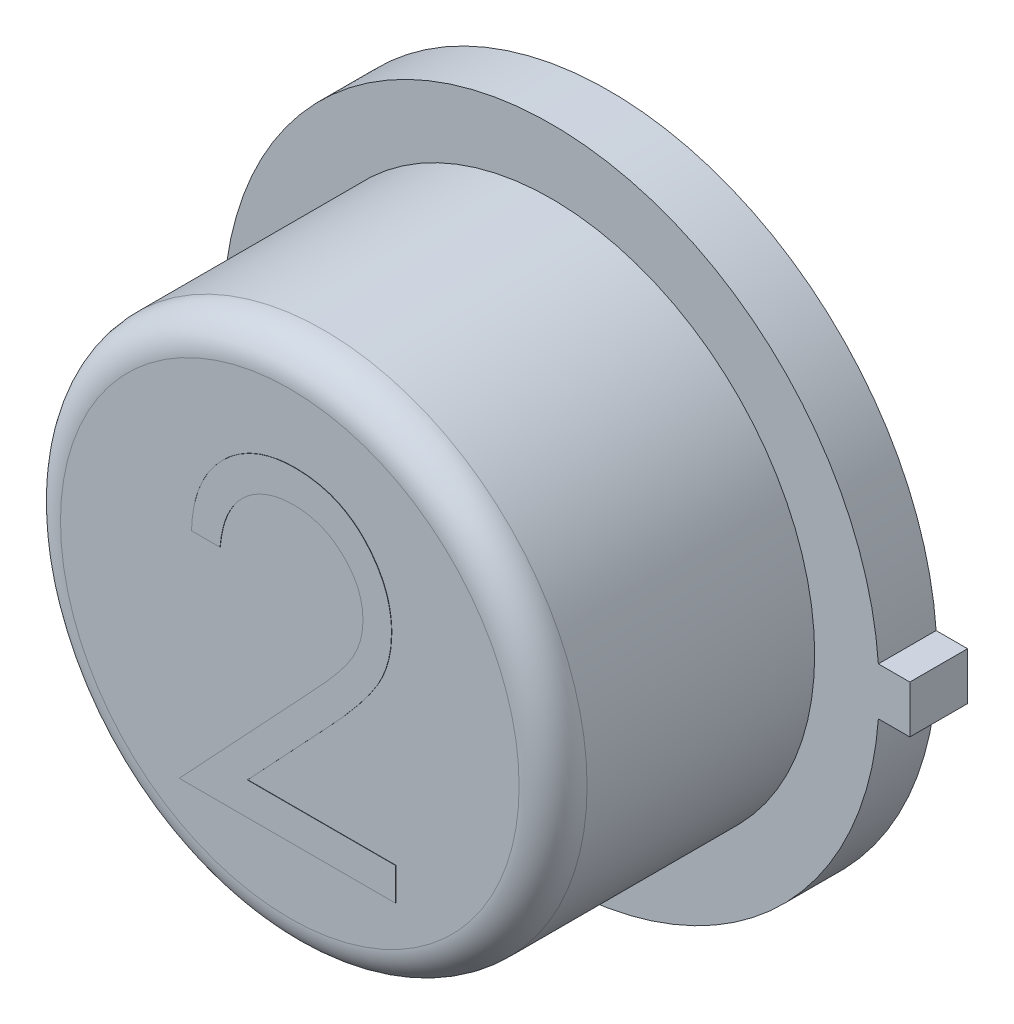
SolidWorks part; units mm, degrees
ref_plane "Front Plane" through (0, 0, 0) normal (0, 0, 1) x (1, 0, 0)
ref_plane "Top Plane" through (0, 0, 0) normal (0, 1, 0) x (1, 0, 0)
ref_plane "Right Plane" through (0, 0, 0) normal (1, 0, 0) x (0, 0, -1)
sketch "Sketch1" plane through (0, 0, 0) normal (0, 0, 1) x (1, 0, 0)
  line L1 (2.4511, 0.1778) -> (2.6797, 0.1778)
  line L3 (2.4511, -0.1778) -> (2.6797, -0.1778)
  line L4 (2.6797, 0.1778) -> (2.6797, -0.1778)
  line L5 (2.4511, 0.1778) -> (2.4444, 0.1778)
  line L6 (2.4511, -0.1778) -> (2.4446, -0.1778)
  arc A0 (2.4446, 0.1778) -> (2.4446, -0.1778) centre (0, 0) ccw
  dimension "D1" = 4.9022
  dimension "D2" = 0.3556
  dimension "D3" = 0.2286
extrude "Boss-Extrude1" add sketch "Sketch1" along normal blind 0.4318
sketch "Sketch2" plane through (0, 0, 0.4318) normal (0, 0, 1) x (1, 0, 0)
  circle A0 centre (0, 0) radius 1.9685
  dimension "D1" = 3.937
extrude "Boss-Extrude2" add sketch "Sketch2" along normal blind 1.9558
sketch "Sketch3" plane through (0, 0, 0) normal (0, 0, -1) x (-1, 0, 0)
  circle A0 centre (0, 0) radius 1.7576
extrude "Boss-Extrude3" add sketch "Sketch3" along normal blind 0.0025
fillet "Fillet1" radius 0.254 1 edges at (1.9685, 0, 2.3876)
sketch "Sketch4" plane through (0, 0, 2.3876) normal (0, 0, 1) x (1, 0, 0)
  line L0 (-1.2065, -1.2181) -> (1.2065, -1.2181) construction
  circle A0 centre (0, 0) radius 1.7145 construction
  text T0 "2" font "Century Gothic" height in points 9
  dimension "D1" = 2.413
extrude "Boss-Extrude5" add sketch "Sketch4" along normal blind 0.0025
